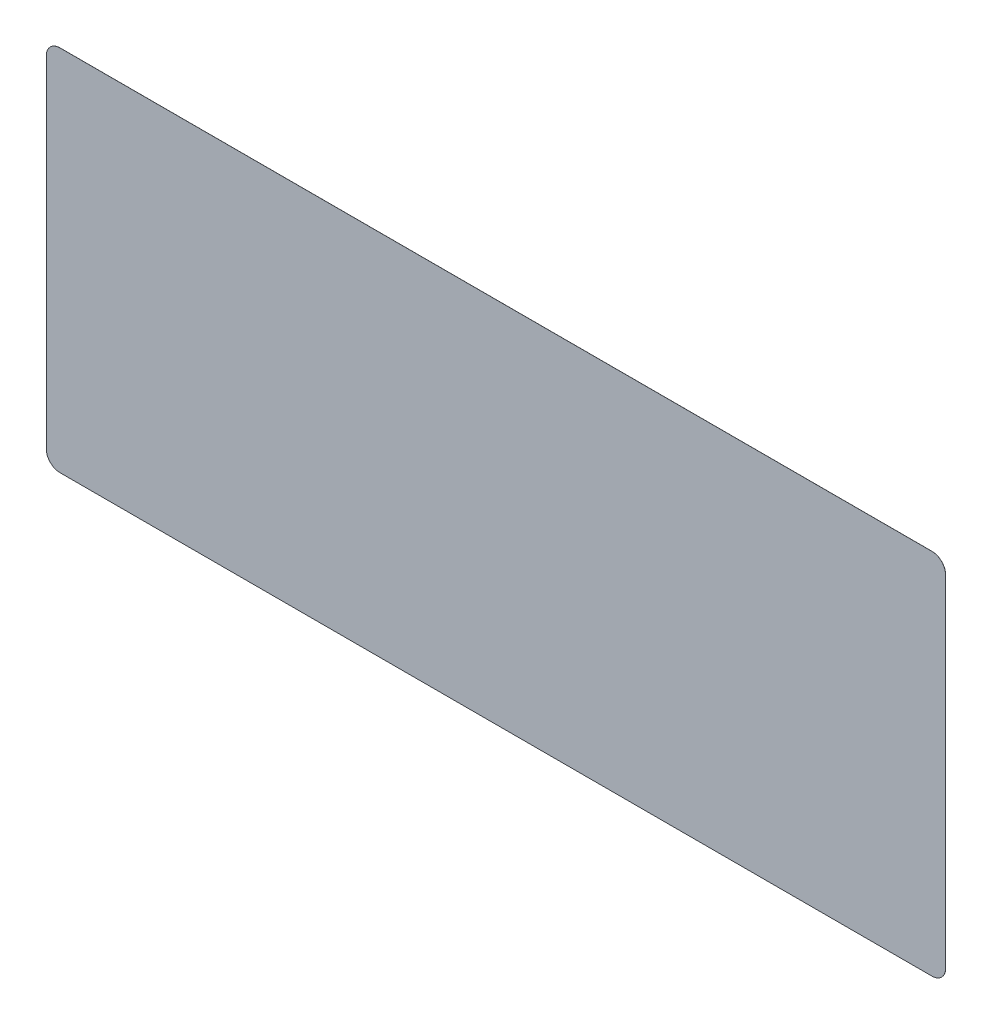
SolidWorks part; units mm, degrees
ref_plane "Front Plane" through (0, 0, 0) normal (0, 0, 1) x (1, 0, 0)
ref_plane "Top Plane" through (0, 0, 0) normal (0, 1, 0) x (1, 0, 0)
ref_plane "Right Plane" through (0, 0, 0) normal (1, 0, 0) x (0, 0, -1)
sketch "Sketch1" plane through (0, 0, 0) normal (0, 0, 1) x (1, 0, 0)
  line L1 (78, 137) -> (206, 137)
  line L2 (76, 135) -> (76, 85)
  line L3 (78, 83) -> (206, 83)
  line L4 (208, 135) -> (208, 85)
  arc A0 (76, 85) -> (78, 83) centre (78, 85) ccw
  arc A1 (206, 137) -> (208, 135) centre (206, 135) cw
  arc A2 (206, 83) -> (208, 85) centre (206, 85) ccw
  arc A3 (78, 137) -> (76, 135) centre (78, 135) ccw
  point P4 (0, 0)
  dimension "D1" = 2
extrude "Boss-Extrude1" add sketch "Sketch1" along normal blind 0.01
